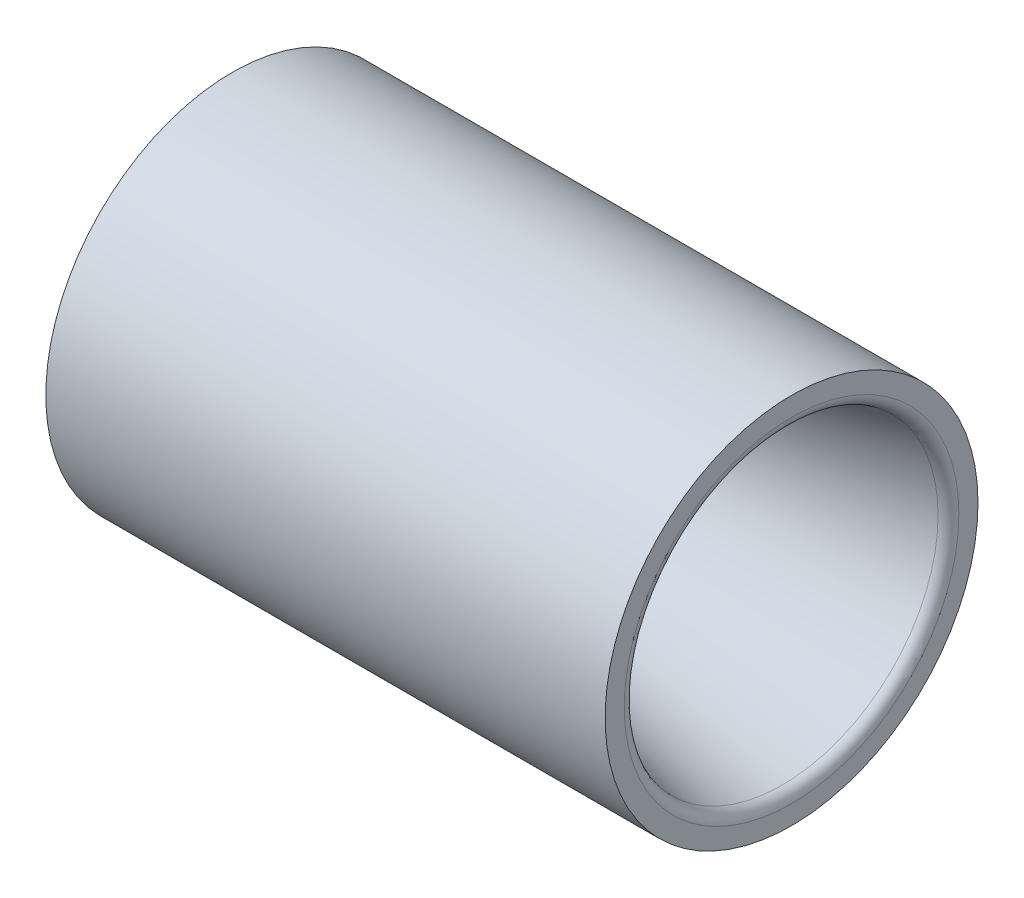
SolidWorks part; units mm, degrees
ref_plane "Front Plane" through (0, 0, 0) normal (0, 0, 1) x (1, 0, 0)
ref_plane "Top Plane" through (0, 0, 0) normal (0, 1, 0) x (1, 0, 0)
ref_plane "Right Plane" through (0, 0, 0) normal (1, 0, 0) x (0, 0, -1)
sketch "Sketch1" plane through (0, 0, 0) normal (0, 1, 0) x (1, 0, 0)
  line L0 (-1.2675, -21.2317) -> (-49.0625, -11.0725)
  line L1 (-51.703, -10.795) -> (-63.5, -10.795)
  line L2 (-63.5, -10.795) -> (-63.5, -9.525)
  line L3 (0, -22.7969) -> (0, -25.4)
  line L4 (0, -25.4) -> (-76.2, -25.4)
  line L5 (-76.2, -25.4) -> (-76.2, -9.525)
  line L6 (-76.2, -9.525) -> (-63.5, -9.525)
  arc A0 (-49.0625, -11.0725) -> (-51.703, -10.795) centre (-51.703, -23.495) ccw
  arc A1 (-1.2675, -21.2317) -> (0, -22.7969) centre (-1.6002, -22.7969) cw
  point P10 (-50.3682, -10.795)
  point P13 (0, -21.5011)
  dimension "D9" = 12.7
  dimension "D10" = 1.6002
  dimension "D1" = 168
  dimension "D2" = 9.525
  dimension "D3" = 63.5
  dimension "D4" = 10.795
  dimension "D5" = 0
  dimension "D6" = 25.4
  dimension "D7" = 50.3682
  dimension "D8" = 76.2
ref_axis "Axis1" through (3.175, 0, 0) along (-1, 0, 0)
revolve "Revolve1" add sketch "Sketch1" angle 360 about axis through (3.175, 0, 0) along (-1, 0, 0)
